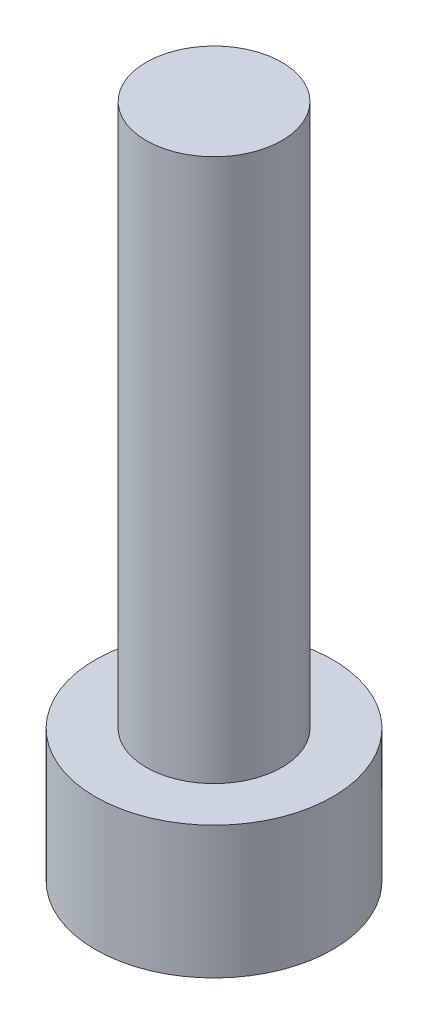
SolidWorks part; units mm, degrees
ref_plane "前视基准面" through (0, 0, 0) normal (0, 0, 1) x (1, 0, 0)
ref_plane "上视基准面" through (0, 0, 0) normal (0, 1, 0) x (1, 0, 0)
ref_plane "右视基准面" through (0, 0, 0) normal (1, 0, 0) x (0, 0, -1)
sketch "草图1" plane through (0, 0, 0) normal (0, 1, 0) x (1, 0, 0)
  circle A0 centre (0, 0) radius 3.5
extrude "凸台-拉伸1" add sketch "草图1" along normal blind 3.9
sketch "草图2" plane through (0, 3.9, 0) normal (0, 1, 0) x (1, 0, 0)
  circle A0 centre (0, 0) radius 2
extrude "凸台-拉伸2" add sketch "草图2" along normal blind 16
sketch "草图3" plane through (0, 0, 0) normal (0, -1, 0) x (1, 0, 0)
  line L1 (1.725, 0) -> (0.8625, 1.4939)
  line L2 (0.8625, 1.4939) -> (-0.8625, 1.4939)
  line L3 (-0.8625, 1.4939) -> (-1.725, 0)
  line L4 (-1.725, 0) -> (-0.8625, -1.4939)
  line L5 (-0.8625, -1.4939) -> (0.8625, -1.4939)
  line L6 (0.8625, -1.4939) -> (1.725, 0)
  circle A0 centre (0, 0) radius 1.4939 construction
extrude "切除-拉伸1" cut sketch "草图3" against normal blind 2.4
